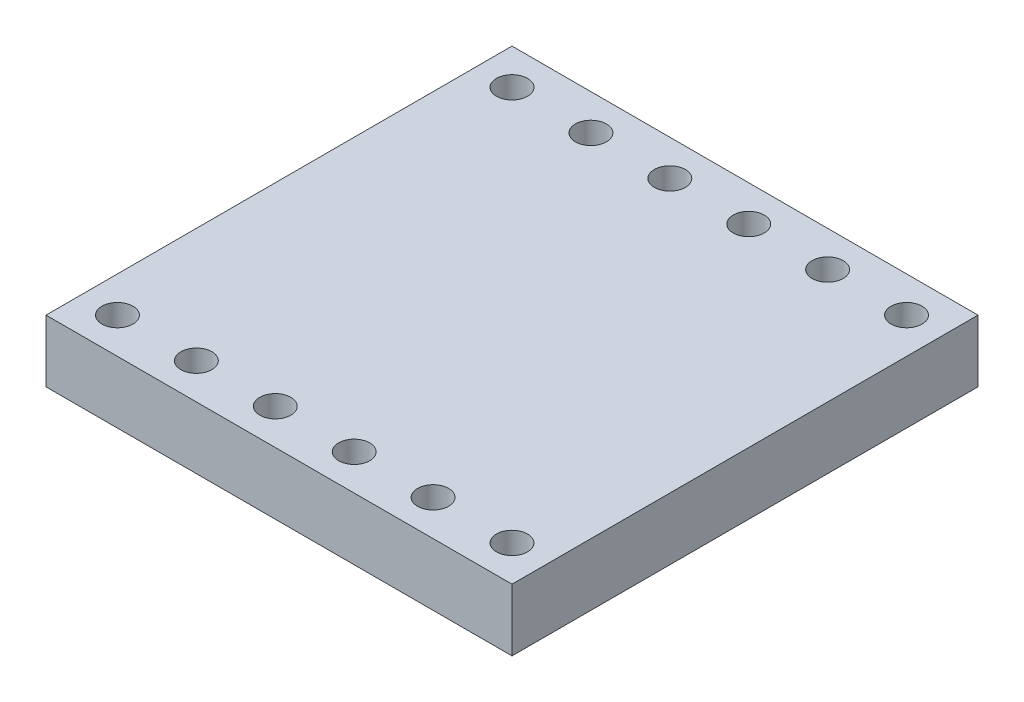
SolidWorks part; units mm, degrees
ref_plane "Front Plane" through (0, 0, 0) normal (0, 0, 1) x (1, 0, 0)
ref_plane "Top Plane" through (0, 0, 0) normal (0, 1, 0) x (1, 0, 0)
ref_plane "Right Plane" through (0, 0, 0) normal (1, 0, 0) x (0, 0, -1)
sketch "Sketch1" plane through (0, 0, 0) normal (0, 1, 0) x (1, 0, 0)
  line L1 (0, 0) -> (15, 0)
  line L2 (0, 0) -> (0, 15)
  line L3 (0, 15) -> (15, 15)
  line L4 (15, 0) -> (15, 15)
  dimension "D1" = 15
  dimension "D2" = 15
extrude "Boss-Extrude1" add sketch "Sketch1" along normal blind 2
sketch "Sketch3" plane through (0, 2, 0) normal (0, 1, 0) x (1, 0, 0)
  line L0 (0, 0) -> (15, 0) construction
  line L1 (15, 0) -> (15, 15) construction
  circle A0 centre (13.85, 1.15) radius 0.5
  circle A1 centre (11.31, 1.15) radius 0.5
  circle A2 centre (8.77, 1.15) radius 0.5
  circle A3 centre (6.23, 1.15) radius 0.5
  circle A4 centre (3.69, 1.15) radius 0.5
  circle A5 centre (1.15, 1.15) radius 0.5
  circle A6 centre (13.85, 13.85) radius 0.5
  circle A7 centre (11.31, 13.85) radius 0.5
  circle A8 centre (8.77, 13.85) radius 0.5
  circle A9 centre (6.23, 13.85) radius 0.5
  circle A10 centre (3.69, 13.85) radius 0.5
  circle A11 centre (1.15, 13.85) radius 0.5
  point P26 (13.4556, 1.15)
  dimension "D1" = 1
  dimension "D3" = 2.54
  dimension "D5" = 12.7
  dimension "D6" = 1.15
  dimension "D7" = 1.15
  dimension "D2" = 6
  dimension "D4" = 2
extrude "Cut-Extrude1" cut sketch "Sketch3" against normal up to surface (2 mm away) up to face at (7.5, 0, -7.5)
